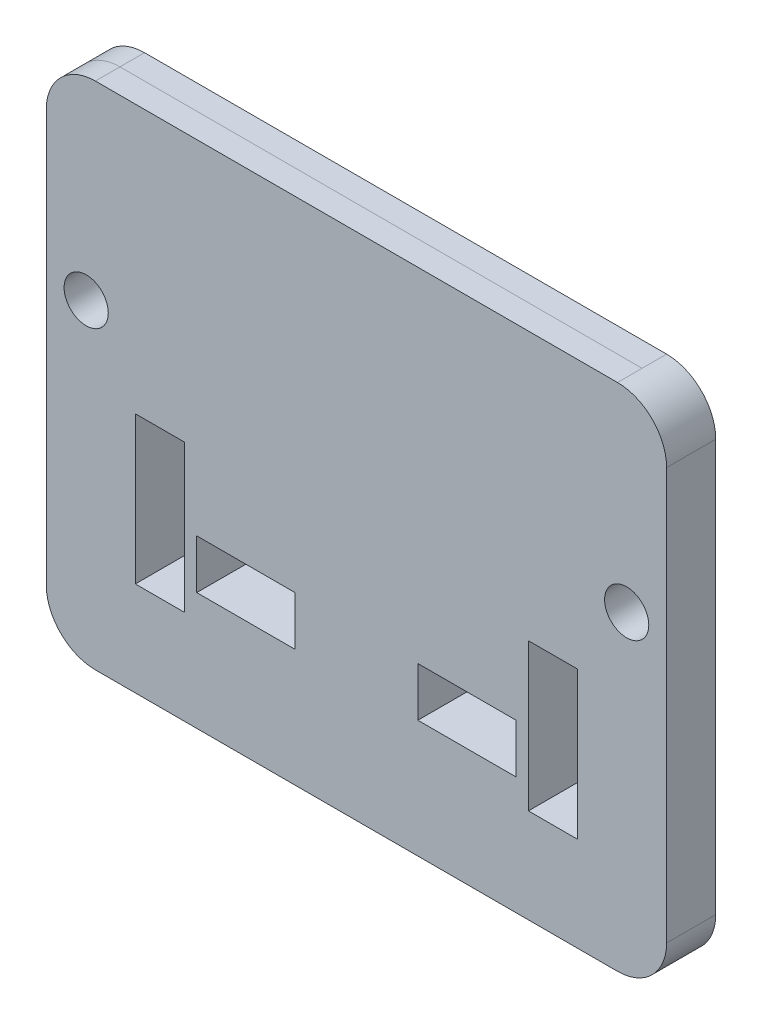
SolidWorks part; units mm, degrees
material "Pink Foam"
ref_plane "Front Plane" through (0, 0, 0) normal (0, 0, 1) x (1, 0, 0)
ref_plane "Top Plane" through (0, 0, 0) normal (0, 1, 0) x (1, 0, 0)
ref_plane "Right Plane" through (0, 0, 0) normal (1, 0, 0) x (0, 0, -1)
sketch "Sketch1" plane through (0, 0, 0) normal (0, 0, 1) x (1, 0, 0)
  line L1 (-139.7, -203.2) -> (139.7, -203.2) construction
  line L2 (-165.1, -177.8) -> (-165.1, 177.8) construction
  line L3 (-139.7, 203.2) -> (139.7, 203.2) construction
  line L4 (165.1, -177.8) -> (165.1, 177.8) construction
  line L5 (-165.1, -203.2) -> (165.1, 203.2) construction
  line L6 (-165.1, 203.2) -> (165.1, -203.2) construction
  line L7 (-134.9375, -131.8019) -> (134.9375, -131.8019)
  line L8 (-160.3375, -106.4019) -> (-160.3375, 106.4019)
  line L9 (-134.9375, 131.8019) -> (134.9375, 131.8019)
  line L10 (160.3375, -106.4019) -> (160.3375, 106.4019)
  line L11 (-160.3375, -131.8019) -> (160.3375, 131.8019) construction
  line L12 (-160.3375, 131.8019) -> (160.3375, -131.8019) construction
  arc A0 (-139.7, -203.2) -> (-165.1, -177.8) centre (-139.7, -177.8) cw construction
  arc A1 (139.7, -203.2) -> (165.1, -177.8) centre (139.7, -177.8) ccw construction
  arc A2 (139.7, 203.2) -> (165.1, 177.8) centre (139.7, 177.8) cw construction
  arc A3 (-165.1, 177.8) -> (-139.7, 203.2) centre (-139.7, 177.8) cw construction
  circle A4 centre (-139.7, 31.2899) radius 11.422
  circle A5 centre (139.7, 31.2899) radius 11.422
  arc A6 (-134.9375, -131.8019) -> (-160.3375, -106.4019) centre (-134.9375, -106.4019) cw
  arc A7 (134.9375, -131.8019) -> (160.3375, -106.4019) centre (134.9375, -106.4019) ccw
  arc A8 (134.9375, 131.8019) -> (160.3375, 106.4019) centre (134.9375, 106.4019) cw
  arc A9 (-160.3375, 106.4019) -> (-134.9375, 131.8019) centre (-134.9375, 106.4019) cw
  point P0 (0, 0)
  point P23 (0, 0)
  dimension "D3" = 25.4
  dimension "D7" = 22.844
  dimension "D8" = 320.6749
  dimension "D10" = 25.4
  dimension "D1" = 330.2
  dimension "D2" = 406.4
  dimension "D4" = 25.4
  dimension "D5" = 100.512
  dimension "D6" = 25.4
  dimension "D9" = 263.6038
extrude "Boss-Extrude1" add sketch "Sketch1" along normal blind 25.4
ref_plane "Plane1" through (0, 0, 12.7) normal (0, 0, 1) x (1, 0, 0)
sketch "Sketch2" plane through (0, 0, 0) normal (0, 0, -1) x (-1, 0, 0)
  line L20 (-82.55, -71) -> (-31.75, -71)
  line L21 (-31.75, -71) -> (-31.75, -45.6)
  line L22 (-31.75, -45.6) -> (-82.55, -45.6)
  line L23 (-82.55, -45.6) -> (-82.55, -71)
  line L32 (31.75, -71) -> (82.55, -71)
  line L33 (31.75, -45.6) -> (31.75, -71)
  line L34 (82.55, -45.6) -> (31.75, -45.6)
  line L35 (82.55, -71) -> (82.55, -45.6)
  dimension "D1" = 31.75
  dimension "D2" = 82.55
  dimension "D3" = 31.75
  dimension "D4" = 45.6
  dimension "D5" = 71
extrude "Foam Insert Cut-Throughs" cut sketch "Sketch2" against normal blind 25.4
split line "Split Line1"
sketch "Sketch3"
  line L8 (-114.3, -6.8101) -> (-114.3, -83.0101)
  line L9 (-88.9, -6.8101) -> (-114.3, -6.8101)
  line L10 (-88.9, -83.0101) -> (-88.9, -6.8101)
  line L11 (-114.3, -83.0101) -> (-88.9, -83.0101)
  line L16 (88.9, -6.8101) -> (88.9, -83.0101)
  line L17 (114.3, -6.8101) -> (88.9, -6.8101)
  line L18 (114.3, -83.0101) -> (114.3, -6.8101)
  line L19 (88.9, -83.0101) -> (114.3, -83.0101)
other "AlignGroup1" parameters "D1"=0, "D2"=0, "D3"=88.9, "D4"=114.3, "D5"=88.9, "D6"=114.3, "D7"=83.0101
other "AlignGroup2"
extrude "Cut-Extrude1" cut sketch "Sketch3" against normal blind 25.4
